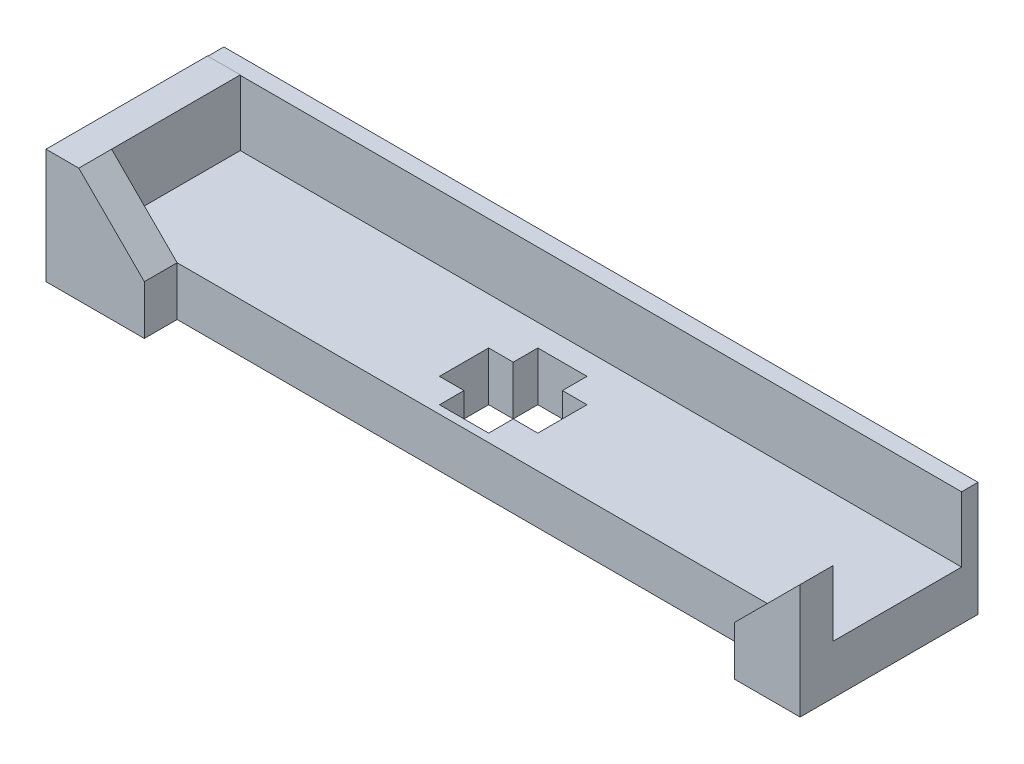
SolidWorks part; units mm, degrees
ref_plane "前视基准面" through (0, 0, 0) normal (0, 0, 1) x (1, 0, 0)
ref_plane "上视基准面" through (0, 0, 0) normal (0, 1, 0) x (1, 0, 0)
ref_plane "右视基准面" through (0, 0, 0) normal (1, 0, 0) x (0, 0, -1)
sketch "草图1" plane through (0, 0, 0) normal (0, 1, 0) x (1, 0, 0)
  line L0 (-35.6129, -6.63) -> (8.3871, -6.63)
  line L1 (-35.6129, -6.63) -> (-35.6129, -14.48)
  line L2 (8.3871, -6.63) -> (8.3871, -14.48)
  line L3 (-35.6129, -14.48) -> (8.3871, -14.48)
  point P6 (11.3492, -12.9146)
  dimension "D1" = 44
  dimension "D2" = 7.85
extrude "凸台-拉伸1" add sketch "草图1" along normal blind 3
sketch "草图2" plane through (-35.6129, 0, 0) normal (-1, 0, 0) x (0, 0, 1)
  line L0 (6.63, 0) -> (14.48, 0)
  line L1 (6.63, 0) -> (6.63, 7)
  line L2 (14.48, 0) -> (14.48, 7)
  line L3 (6.63, 7) -> (14.48, 7)
  dimension "D1" = 7
extrude "凸台-拉伸2" add sketch "草图2" along normal blind 2
sketch "草图3" plane through (0, 0, 14.48) normal (0, 0, 1) x (1, 0, 0)
  line L0 (-35.6129, 7) -> (-31.6129, 3)
  line L1 (-35.6129, 3) -> (8.3871, 3) construction
  line L2 (-31.6129, 3) -> (-31.6129, 0)
  line L3 (-37.6129, 0) -> (8.3871, 0) construction
  line L4 (-31.6129, 0) -> (-35.6129, 0)
  line L5 (-35.6129, 0) -> (-37.6129, 0)
  line L6 (-37.6129, 0) -> (-37.6129, 7)
  line L7 (-37.6129, 7) -> (-35.6129, 7)
  dimension "D1" = 4
  dimension "D2" = 4
extrude "凸台-拉伸3" add sketch "草图3" along normal blind 2
sketch "草图4" plane through (0, 0, 14.48) normal (0, 0, 1) x (1, 0, 0)
  line L0 (8.3871, 0) -> (8.3871, 7)
  line L1 (8.3871, 7) -> (4.3871, 3)
  line L2 (-31.6129, 3) -> (8.3871, 3) construction
  line L3 (4.3871, 3) -> (4.3871, 0)
  line L4 (-31.6129, 0) -> (8.3871, 0) construction
  line L5 (4.3871, 0) -> (8.3871, 0)
  dimension "D1" = 4
extrude "凸台-拉伸4" add sketch "草图4" along normal blind 2
sketch "草图5" plane through (0, 0, 6.63) normal (0, 0, -1) x (-1, 0, 0)
  line L0 (-8.3871, 0) -> (37.6129, 0)
  line L1 (-8.3871, 0) -> (-8.3871, 6.9765)
  line L2 (37.6129, 0) -> (37.6129, 6.9765)
  line L3 (-8.3871, 6.9765) -> (37.6129, 6.9765)
extrude "凸台-拉伸5" add sketch "草图5" along normal blind 1
sketch "草图6" plane through (0, 0, 0) normal (0, -1, 0) x (1, 0, 0)
  line L0 (-17.6129, 12.48) -> (-11.6129, 12.48)
  line L1 (-17.6129, 12.48) -> (-17.6129, 9.48)
  line L2 (-11.6129, 12.48) -> (-11.6129, 9.48)
  line L3 (-17.6129, 9.48) -> (-11.6129, 9.48)
  line L4 (-31.6129, 14.48) -> (4.3871, 14.48) construction
  line L5 (8.3871, 16.48) -> (8.3871, 5.63) construction
  point P6 (8.3871, 11.055)
  dimension "D1" = 3
  dimension "D2" = 6
  dimension "D3" = 2
  dimension "D4" = 20
extrude "切除-拉伸3" cut sketch "草图6" against normal blind 3
sketch "草图8" plane through (0, 0, 0) normal (0, -1, 0) x (1, 0, 0)
  line L0 (-16.1129, 13.98) -> (-16.1129, 7.98)
  line L1 (-16.1129, 13.98) -> (-13.1129, 13.98)
  line L2 (-16.1129, 7.98) -> (-13.1129, 7.98)
  line L3 (-13.1129, 13.98) -> (-13.1129, 7.98)
  line L4 (-11.6129, 12.48) -> (-17.6129, 12.48) construction
  line L5 (-17.6129, 9.48) -> (-11.6129, 9.48) construction
  line L6 (-11.6129, 9.48) -> (-11.6129, 12.48) construction
  line L7 (-17.6129, 12.48) -> (-17.6129, 9.48) construction
  dimension "D1" = 1.5
  dimension "D2" = 1.5
  dimension "D3" = 1.5
  dimension "D4" = 1.5
extrude "切除-拉伸4" cut sketch "草图8" against normal blind 3
